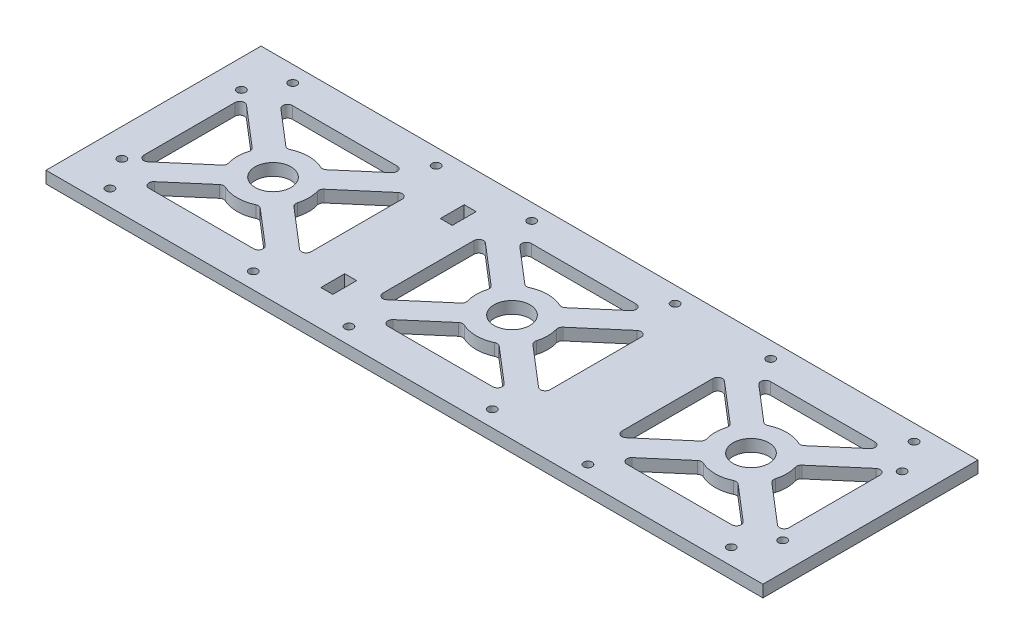
SolidWorks part; units mm, degrees
ref_plane "Front Plane" through (0, 0, 0) normal (0, 0, 1) x (1, 0, 0)
ref_plane "Top Plane" through (0, 0, 0) normal (0, 1, 0) x (1, 0, 0)
ref_plane "Right Plane" through (0, 0, 0) normal (1, 0, 0) x (0, 0, -1)
sketch "Sketch1" plane through (0, 0, 0) normal (0, 1, 0) x (1, 0, 0)
  line L0 (-966.8368, 0) -> (47375.0043, 0) construction
  line L1 (-21.9105, 30) -> (21.9105, 30)
  line L2 (-35, 19.0662) -> (-35, -19.0662)
  line L3 (-21.9105, -30) -> (21.9105, -30)
  line L4 (35, 19.0662) -> (35, -19.0662)
  line L5 (-35, 30) -> (35, -30) construction
  line L6 (-35, -30) -> (35, 30) construction
  line L7 (-50, 45) -> (150, 45)
  line L8 (-50, 45) -> (-50, -45) construction
  line L9 (-50, -45) -> (150, -45)
  line L10 (50, 45) -> (50, -45) construction
  line L11 (-50, 45) -> (50, -45) construction
  line L12 (-50, -45) -> (50, 45) construction
  line L13 (-31.6984, 20.5847) -> (-15.0163, 6.2857)
  line L14 (-23.2121, 26.4815) -> (-8.5084, 13.8783)
  line L15 (0, -1000) -> (0, 49000) construction
  line L16 (23.2121, 26.4815) -> (8.5084, 13.8783)
  line L17 (31.6984, 20.5847) -> (15.0163, 6.2857)
  line L18 (31.6984, -20.5847) -> (15.0163, -6.2857)
  line L19 (23.2121, -26.4815) -> (8.5084, -13.8783)
  line L20 (-23.2121, -26.4815) -> (-8.5084, -13.8783)
  line L21 (-31.6984, -20.5847) -> (-15.0163, -6.2857)
  line L22 (-35, 30) -> (-35, 23.4146) construction
  line L23 (-23.8844, 30) -> (-27.317, 30) construction
  line L24 (27.317, 30) -> (35, 30) construction
  line L25 (35, 30) -> (35, 23.4146) construction
  line L26 (35, -23.4146) -> (35, -30) construction
  line L27 (27.317, -30) -> (35, -30) construction
  line L28 (-35, -30) -> (-27.317, -30) construction
  line L29 (-35, -23.4146) -> (-35, -30) construction
  line L30 (135, -23.4146) -> (135, -30) construction
  line L31 (135, -30) -> (127.317, -30) construction
  line L32 (72.683, -30) -> (65, -30) construction
  line L33 (65, -23.4146) -> (65, -30) construction
  line L34 (65, 30) -> (65, 23.4146) construction
  line L35 (72.683, 30) -> (65, 30) construction
  line L36 (123.8844, 30) -> (127.317, 30) construction
  line L37 (135, 30) -> (135, 23.4146) construction
  line L38 (100, -1000) -> (100, 49000) construction
  line L39 (150, -45) -> (50, 45) construction
  line L40 (150, 45) -> (50, -45) construction
  line L41 (135, -30) -> (65, 30) construction
  line L42 (135, 30) -> (65, -30) construction
  line L43 (1066.8368, 0) -> (-47275.0043, 0) construction
  line L44 (131.6984, -20.5847) -> (115.0163, -6.2857)
  line L45 (123.2121, -26.4815) -> (108.5084, -13.8783)
  line L46 (76.7879, -26.4815) -> (91.4916, -13.8783)
  line L47 (68.3016, -20.5847) -> (84.9837, -6.2857)
  line L48 (68.3016, 20.5847) -> (84.9837, 6.2857)
  line L49 (76.7879, 26.4815) -> (91.4916, 13.8783)
  line L50 (123.2121, 26.4815) -> (108.5084, 13.8783)
  line L51 (131.6984, 20.5847) -> (115.0163, 6.2857)
  line L52 (150, 45) -> (150, -45)
  line L53 (65, 19.0662) -> (65, -19.0662)
  line L54 (121.9105, -30) -> (78.0895, -30)
  line L55 (135, 19.0662) -> (135, -19.0662)
  line L56 (121.9105, 30) -> (78.0895, 30)
  line L57 (-1166.8368, 0) -> (47175.0043, 0) construction
  line L58 (-65, -23.4146) -> (-65, -30) construction
  line L59 (-65, -30) -> (-72.683, -30) construction
  line L60 (-127.317, -30) -> (-135, -30) construction
  line L61 (-135, -23.4146) -> (-135, -30) construction
  line L62 (-135, 30) -> (-135, 23.4146) construction
  line L63 (-127.317, 30) -> (-135, 30) construction
  line L64 (-76.1156, 30) -> (-72.683, 30) construction
  line L65 (-65, 30) -> (-65, 23.4146) construction
  line L66 (-100, -1000) -> (-100, 49000) construction
  line L67 (-50, -45) -> (-150, 45) construction
  line L68 (-50, 45) -> (-150, -45) construction
  line L69 (-65, -30) -> (-135, 30) construction
  line L70 (-65, 30) -> (-135, -30) construction
  line L71 (866.8368, 0) -> (-47475.0043, 0) construction
  line L72 (-68.3016, -20.5847) -> (-84.9837, -6.2857)
  line L73 (-76.7879, -26.4815) -> (-91.4916, -13.8783)
  line L74 (-123.2121, -26.4815) -> (-108.5084, -13.8783)
  line L75 (-131.6984, -20.5847) -> (-115.0163, -6.2857)
  line L76 (-131.6984, 20.5847) -> (-115.0163, 6.2857)
  line L77 (-123.2121, 26.4815) -> (-108.5084, 13.8783)
  line L78 (-76.7879, 26.4815) -> (-91.4916, 13.8783)
  line L79 (-68.3016, 20.5847) -> (-84.9837, 6.2857)
  line L80 (-50, -45) -> (-150, -45)
  line L81 (-50, 45) -> (-150, 45)
  line L82 (-135, 19.0662) -> (-135, -19.0662)
  line L83 (-78.0895, -30) -> (-121.9105, -30)
  line L84 (-65, 19.0662) -> (-65, -19.0662)
  line L85 (-78.0895, 30) -> (-121.9105, 30)
  line L86 (-150, 45) -> (-150, -45)
  line L88 (-140, 40) -> (140, 40) construction
  line L89 (-140, 40) -> (-140, -40) construction
  line L90 (-140, -40) -> (140, -40) construction
  line L91 (140, 40) -> (140, -40) construction
  line L92 (-140, 40) -> (140, -40) construction
  line L93 (-140, -40) -> (140, 40) construction
  line L161 (-50, 30) -> (-50, 20)
  line L162 (-50, 30) -> (-45, 30)
  line L163 (-50, -30) -> (-45, -30)
  line L164 (-50, -20) -> (-45, -20)
  line L165 (-50, 20) -> (-45, 20)
  line L166 (-50, -30) -> (-50, -20)
  line L167 (-45, 30) -> (-45, 20)
  line L168 (-45, -30) -> (-45, -20)
  circle A0 centre (0, 0) radius 7.5
  arc A1 (-6.359, -13.5854) -> (6.359, -13.5854) centre (0, 0) ccw
  arc A2 (-13.9915, -5.4073) -> (-11.3888, -9.7619) centre (0, 0) ccw construction
  arc A3 (-11.3888, -9.7619) -> (-7.4836, -12.9999) centre (0, 0) ccw construction
  arc A4 (-11.3888, 9.7619) -> (-13.9915, 5.4073) centre (0, 0) ccw construction
  arc A5 (-14.3981, 4.2064) -> (-14.3981, -4.2064) centre (0, 0) ccw
  arc A6 (-7.4836, 12.9999) -> (-11.3888, 9.7619) centre (0, 0) ccw construction
  arc A7 (11.3888, 9.7619) -> (7.4836, 12.9999) centre (0, 0) ccw construction
  arc A8 (6.359, 13.5854) -> (-6.359, 13.5854) centre (0, 0) ccw
  arc A9 (13.9915, 5.4073) -> (11.3888, 9.7619) centre (0, 0) ccw construction
  arc A10 (11.3888, -9.7619) -> (13.9915, -5.4073) centre (0, 0) ccw construction
  arc A11 (14.3981, -4.2064) -> (14.3981, 4.2064) centre (0, 0) ccw
  arc A12 (7.4836, -12.9999) -> (11.3888, -9.7619) centre (0, 0) ccw construction
  arc A13 (-14.3981, 4.2064) -> (-15.0163, 6.2857) centre (-16.3179, 4.7672) ccw
  arc A14 (-14.3981, -4.2064) -> (-15.0163, -6.2857) centre (-16.3179, -4.7672) cw
  arc A15 (-31.6984, -20.5847) -> (-35, -19.0662) centre (-33, -19.0662) cw
  arc A16 (-31.6984, 20.5847) -> (-35, 19.0662) centre (-33, 19.0662) ccw
  arc A17 (-21.9105, -30) -> (-23.2121, -26.4815) centre (-21.9105, -28) cw
  arc A18 (21.9105, -30) -> (23.2121, -26.4815) centre (21.9105, -28) ccw
  arc A19 (8.5084, -13.8783) -> (6.359, -13.5854) centre (7.2068, -15.3968) ccw
  arc A20 (-6.359, -13.5854) -> (-8.5084, -13.8783) centre (-7.2068, -15.3968) ccw
  arc A21 (35, 19.0662) -> (31.6984, 20.5847) centre (33, 19.0662) ccw
  arc A22 (35, -19.0662) -> (31.6984, -20.5847) centre (33, -19.0662) cw
  arc A23 (15.0163, -6.2857) -> (14.3981, -4.2064) centre (16.3179, -4.7672) cw
  arc A24 (14.3981, 4.2064) -> (15.0163, 6.2857) centre (16.3179, 4.7672) cw
  arc A25 (8.5084, 13.8783) -> (6.359, 13.5854) centre (7.2068, 15.3968) cw
  arc A26 (-6.359, 13.5854) -> (-8.5084, 13.8783) centre (-7.2068, 15.3968) cw
  arc A27 (21.9105, 30) -> (23.2121, 26.4815) centre (21.9105, 28) cw
  arc A28 (-21.9105, 30) -> (-23.2121, 26.4815) centre (-21.9105, 28) ccw
  arc A29 (92.5164, -12.9999) -> (88.6112, -9.7619) centre (100, 0) cw construction
  arc A30 (88.6112, -9.7619) -> (86.0085, -5.4073) centre (100, 0) cw construction
  arc A31 (86.0085, 5.4073) -> (88.6112, 9.7619) centre (100, 0) cw construction
  arc A32 (88.6112, 9.7619) -> (92.5164, 12.9999) centre (100, 0) cw construction
  arc A33 (107.4836, 12.9999) -> (111.3888, 9.7619) centre (100, 0) cw construction
  arc A34 (111.3888, 9.7619) -> (113.9915, 5.4073) centre (100, 0) cw construction
  arc A35 (111.3888, -9.7619) -> (107.4836, -12.9999) centre (100, 0) cw construction
  arc A36 (113.9915, -5.4073) -> (111.3888, -9.7619) centre (100, 0) cw construction
  arc A37 (121.9105, 30) -> (123.2121, 26.4815) centre (121.9105, 28) cw
  arc A38 (78.0895, 30) -> (76.7879, 26.4815) centre (78.0895, 28) ccw
  arc A39 (106.359, 13.5854) -> (108.5084, 13.8783) centre (107.2068, 15.3968) ccw
  arc A40 (91.4916, 13.8783) -> (93.641, 13.5854) centre (92.7932, 15.3968) ccw
  arc A41 (85.6019, 4.2064) -> (84.9837, 6.2857) centre (83.6821, 4.7672) ccw
  arc A42 (84.9837, -6.2857) -> (85.6019, -4.2064) centre (83.6821, -4.7672) ccw
  arc A43 (65, -19.0662) -> (68.3016, -20.5847) centre (67, -19.0662) ccw
  arc A44 (65, 19.0662) -> (68.3016, 20.5847) centre (67, 19.0662) cw
  arc A45 (106.359, -13.5854) -> (108.5084, -13.8783) centre (107.2068, -15.3968) cw
  arc A46 (91.4916, -13.8783) -> (93.641, -13.5854) centre (92.7932, -15.3968) cw
  arc A47 (78.0895, -30) -> (76.7879, -26.4815) centre (78.0895, -28) cw
  arc A48 (121.9105, -30) -> (123.2121, -26.4815) centre (121.9105, -28) ccw
  arc A49 (131.6984, 20.5847) -> (135, 19.0662) centre (133, 19.0662) cw
  arc A50 (131.6984, -20.5847) -> (135, -19.0662) centre (133, -19.0662) ccw
  arc A51 (114.3981, -4.2064) -> (115.0163, -6.2857) centre (116.3179, -4.7672) ccw
  arc A52 (114.3981, 4.2064) -> (115.0163, 6.2857) centre (116.3179, 4.7672) cw
  arc A53 (85.6019, -4.2064) -> (85.6019, 4.2064) centre (100, 0) cw
  arc A54 (93.641, 13.5854) -> (106.359, 13.5854) centre (100, 0) cw
  arc A55 (114.3981, 4.2064) -> (114.3981, -4.2064) centre (100, 0) cw
  arc A56 (106.359, -13.5854) -> (93.641, -13.5854) centre (100, 0) cw
  circle A57 centre (100, 0) radius 7.5
  arc A58 (-107.4836, -12.9999) -> (-111.3888, -9.7619) centre (-100, 0) cw construction
  arc A59 (-111.3888, -9.7619) -> (-113.9915, -5.4073) centre (-100, 0) cw construction
  arc A60 (-113.9915, 5.4073) -> (-111.3888, 9.7619) centre (-100, 0) cw construction
  arc A61 (-111.3888, 9.7619) -> (-107.4836, 12.9999) centre (-100, 0) cw construction
  arc A62 (-92.5164, 12.9999) -> (-88.6112, 9.7619) centre (-100, 0) cw construction
  arc A63 (-88.6112, 9.7619) -> (-86.0085, 5.4073) centre (-100, 0) cw construction
  arc A64 (-88.6112, -9.7619) -> (-92.5164, -12.9999) centre (-100, 0) cw construction
  arc A65 (-86.0085, -5.4073) -> (-88.6112, -9.7619) centre (-100, 0) cw construction
  arc A66 (-78.0895, 30) -> (-76.7879, 26.4815) centre (-78.0895, 28) cw
  arc A67 (-121.9105, 30) -> (-123.2121, 26.4815) centre (-121.9105, 28) ccw
  arc A68 (-93.641, 13.5854) -> (-91.4916, 13.8783) centre (-92.7932, 15.3968) ccw
  arc A69 (-108.5084, 13.8783) -> (-106.359, 13.5854) centre (-107.2068, 15.3968) ccw
  arc A70 (-114.3981, 4.2064) -> (-115.0163, 6.2857) centre (-116.3179, 4.7672) ccw
  arc A71 (-115.0163, -6.2857) -> (-114.3981, -4.2064) centre (-116.3179, -4.7672) ccw
  arc A72 (-135, -19.0662) -> (-131.6984, -20.5847) centre (-133, -19.0662) ccw
  arc A73 (-135, 19.0662) -> (-131.6984, 20.5847) centre (-133, 19.0662) cw
  arc A74 (-93.641, -13.5854) -> (-91.4916, -13.8783) centre (-92.7932, -15.3968) cw
  arc A75 (-108.5084, -13.8783) -> (-106.359, -13.5854) centre (-107.2068, -15.3968) cw
  arc A76 (-121.9105, -30) -> (-123.2121, -26.4815) centre (-121.9105, -28) cw
  arc A77 (-78.0895, -30) -> (-76.7879, -26.4815) centre (-78.0895, -28) ccw
  arc A78 (-68.3016, 20.5847) -> (-65, 19.0662) centre (-67, 19.0662) cw
  arc A79 (-68.3016, -20.5847) -> (-65, -19.0662) centre (-67, -19.0662) ccw
  arc A80 (-85.6019, -4.2064) -> (-84.9837, -6.2857) centre (-83.6821, -4.7672) ccw
  arc A81 (-85.6019, 4.2064) -> (-84.9837, 6.2857) centre (-83.6821, 4.7672) cw
  arc A82 (-114.3981, -4.2064) -> (-114.3981, 4.2064) centre (-100, 0) cw
  arc A83 (-106.359, 13.5854) -> (-93.641, 13.5854) centre (-100, 0) cw
  arc A84 (-85.6019, 4.2064) -> (-85.6019, -4.2064) centre (-100, 0) cw
  arc A85 (-93.641, -13.5854) -> (-106.359, -13.5854) centre (-100, 0) cw
  circle A86 centre (-100, 0) radius 7.5
  circle A87 centre (-138.25, 25) radius 1.75
  circle A88 centre (-130, 38.25) radius 1.75
  circle A89 centre (-138.25, -25) radius 1.75
  circle A90 centre (-70, 38.25) radius 1.75
  circle A91 centre (-30, 38.25) radius 1.75
  circle A92 centre (30, 38.25) radius 1.75
  circle A93 centre (70, 38.25) radius 1.75
  circle A94 centre (130, 38.25) radius 1.75
  circle A95 centre (-130, -38.25) radius 1.75
  circle A96 centre (-70, -38.25) radius 1.75
  circle A97 centre (-30, -38.25) radius 1.75
  circle A98 centre (30, -38.25) radius 1.75
  circle A99 centre (70, -38.25) radius 1.75
  circle A100 centre (130, -38.25) radius 1.75
  circle A101 centre (138.25, -25) radius 1.75
  circle A102 centre (138.25, 25) radius 1.75
  dimension "D5" = 30
  dimension "D6" = 15
  dimension "D1" = 2
  dimension "D8" = 2
  dimension "D13" = 3.5
  dimension "D15" = 3.5
  dimension "1.5" = 15
  dimension "D2" = 15
  dimension "D3" = 100
  dimension "D4" = 90
  dimension "D7" = 5
  dimension "0.5" = 5
  dimension "D9" = 15
  dimension "D10" = 100
  dimension "D11" = 100
  dimension "D12" = 80
  dimension "D14" = 15
  dimension "D16" = 10
  dimension "D19" = 40
  dimension "D20" = 5
  dimension "D21" = 10
  dimension "D22" = 10
  dimension "D23" = 5
  dimension "D24" = 15
  dimension "D25" = 10
  dimension "D26" = 90
  dimension "D27" = 280
extrude "Boss-Extrude2" add sketch "Sketch1" along normal blind 5
